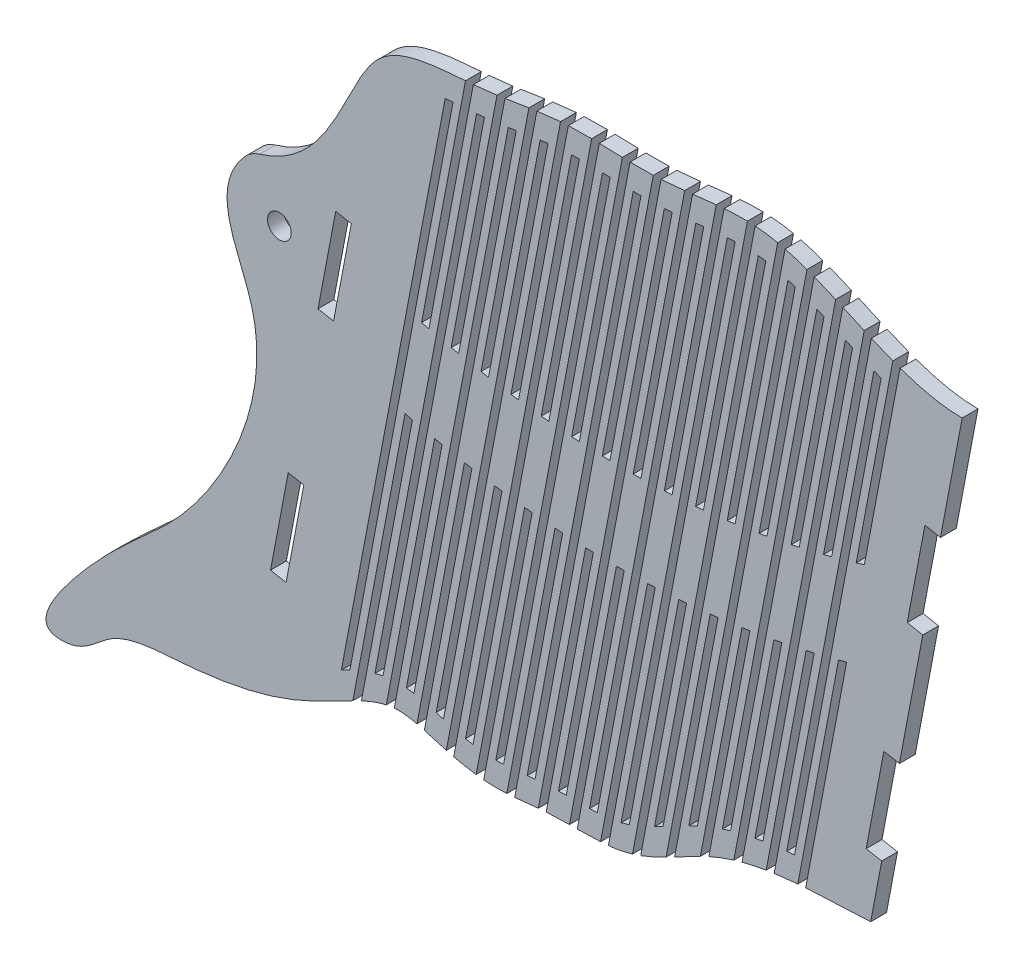
SolidWorks part; units mm, degrees
ref_plane "Front Plane" through (0, 0, 0) normal (0, 0, 1) x (1, 0, 0)
ref_plane "Top Plane" through (0, 0, 0) normal (0, 1, 0) x (1, 0, 0)
ref_plane "Right Plane" through (0, 0, 0) normal (1, 0, 0) x (0, 0, -1)
sketch "Sketch1" plane through (0, 0, 0) normal (0, 0, 1) x (1, 0, 0)
  line L0 (302.5, 350) -> (1512.5, 350) construction
  line L1 (262.9659, 222.1766) -> (281.3274, 318.909)
  line L2 (265.1799, 233.8401) -> (262.0606, 234.4322)
  line L3 (262.0606, 234.4322) -> (265.6131, 253.148)
  line L4 (265.6131, 253.148) -> (268.7324, 252.5559)
  line L5 (270.2997, 277.8379) -> (273.419, 277.2458)
  line L6 (270.2997, 277.8379) -> (273.8523, 296.5537)
  line L7 (273.8523, 296.5537) -> (276.9716, 295.9616)
  circle A0 centre (144.2993, 283.7368) radius 2.3813
  arc A1 (140.318, 294.2582) -> (137.3931, 292.395) centre (142.1375, 288.1744) ccw
  spline S0 degree 3 poles (140.318, 294.2582) (144.6102, 295.5419) (152.0973, 300.9004) (157.8753, 312.5659) (165.4859, 327.6166) (184.0324, 327.0096) (201.9177, 331.2233) (220.7397, 328.9762) (248.5279, 335.4047) (266.9458, 318.9101) (281.3274, 318.909) knots 0.008505 0.008505 0.008505 0.008505 0.084335 0.182889 0.2513 0.382138 0.48334 0.605315 0.73297 1 1 1 1
  spline S1 degree 3 poles (262.9659, 222.1766) (252.7762, 221.635) (234.6147, 222.0465) (215.7154, 207.8397) (199.7769, 209.3976) (187.3708, 207.1634) (177.2277, 209.3133) (167.4809, 212.7163) (157.835, 208.1386) (144.6841, 200.9083) (128.176, 197.8077) (111.1887, 197.5614) (105.0884, 189.8759) (93.8703, 189.645) (109.3047, 211.1797) (127.8117, 222.333) (145.742, 257.3878) (132.8133, 279.6418) (133.8098, 288.3669) (137.3931, 292.395) knots 0 0 0 0 0.108343 0.179805 0.231481 0.269558 0.310048 0.338876 0.372966 0.414981 0.496706 0.548446 0.578687 0.594262 0.641813 0.740934 0.901271 0.95171 0.994791 0.994791 0.994791 0.994791
  dimension "D1" = 6.35
  dimension "D10" = 4.7625
  dimension "D2" = 262.9659
  dimension "D3" = 281.3274
  dimension "D4" = 222.1766
  dimension "D5" = 318.909
  dimension "D6" = 3.175
  dimension "D7" = 3.175
  dimension "D8" = 19.05
  dimension "D9" = 19.05
extrude "Boss-Extrude1" add sketch "Sketch1" along normal blind 3.175 contours S1 L1 L2 L3 L4 L5 L6 L7 S0 A1 A0
sketch "Sketch2" plane through (0, 0, 3.175) normal (0, 0, 1) x (1, 0, 0)
  line L0 (255.132, 281.6956) -> (265.1753, 334.6059)
  line L1 (246.7613, 204.9081) -> (258.1468, 264.8897)
  line L2 (245.215, 204.934) -> (256.5109, 264.4431)
  line L3 (247.691, 226.15) -> (265.0641, 317.6756)
  line L4 (246.1113, 226) -> (263.6224, 318.2528)
  line L5 (240.5761, 205.0117) -> (251.6222, 263.205)
  line L6 (239.0298, 205.0376) -> (249.999, 262.8258)
  line L7 (241.3378, 225.3689) -> (259.32, 320.103)
  line L8 (239.7325, 225.0838) -> (257.89, 320.7417)
  line L9 (234.3909, 205.1154) -> (245.1483, 261.7877)
  line L10 (232.8446, 205.1413) -> (243.5376, 261.4744)
  line L11 (234.86, 223.9309) -> (253.5981, 322.6474)
  line L12 (233.213, 223.4259) -> (252.163, 323.2591)
  line L13 (228.2057, 205.219) -> (238.7239, 260.6311)
  line L14 (226.6595, 205.2449) -> (237.1254, 260.382)
  line L15 (228.1827, 221.4417) -> (247.8261, 324.9276)
  line L16 (226.4759, 220.6222) -> (246.3653, 325.4039)
  line L17 (222.0206, 205.3226) -> (232.3478, 259.7287)
  line L18 (220.4743, 205.3485) -> (230.7611, 259.542)
  line L19 (221.3104, 217.9258) -> (241.9148, 326.4739)
  line L20 (219.5905, 217.0368) -> (240.4024, 326.6783)
  line L21 (215.8354, 205.4262) -> (226.0187, 259.074)
  line L22 (214.2891, 205.4521) -> (224.4436, 258.9484)
  line L23 (214.5179, 214.8296) -> (235.7695, 326.7879)
  line L24 (212.8743, 214.3431) -> (234.2014, 326.6988)
  line L25 (209.6502, 205.5298) -> (219.7355, 258.6612)
  line L26 (208.1039, 205.5557) -> (218.1717, 258.5951)
  line L27 (208.0992, 213.7032) -> (229.4592, 326.2325)
  line L28 (206.5372, 213.6462) -> (227.8731, 326.0484)
  line L29 (203.465, 205.6334) -> (213.497, 258.4843)
  line L30 (201.9187, 205.6593) -> (211.9443, 258.4763)
  line L31 (201.8749, 213.6006) -> (223.1248, 325.55)
  line L32 (200.3182, 213.5718) -> (221.551, 325.4306)
  line L33 (197.2798, 205.737) -> (207.3024, 258.5379)
  line L34 (195.7335, 205.7629) -> (205.7604, 258.5866)
  line L35 (195.6074, 213.2705) -> (216.8695, 325.284)
  line L36 (194.0253, 213.1078) -> (215.32, 325.293)
  line L37 (191.0946, 205.8406) -> (201.1504, 258.8165)
  line L38 (189.5484, 205.8665) -> (199.619, 258.9207)
  line L39 (189.292, 212.688) -> (210.6879, 325.4063)
  line L40 (187.734, 212.6525) -> (209.1452, 325.4513)
  line L41 (184.9095, 205.9442) -> (195.0402, 259.315)
  line L42 (183.3632, 205.9701) -> (193.519, 259.4734)
  line L43 (183.1602, 213.0731) -> (204.5019, 325.5058)
  line L44 (181.663, 213.3573) -> (202.9437, 325.4688)
  line L45 (178.7243, 206.0478) -> (188.9708, 260.0285)
  line L46 (177.178, 206.0737) -> (187.4597, 260.2399)
  line L47 (177.2251, 214.4939) -> (198.2146, 325.0716)
  line L48 (175.7571, 214.9322) -> (196.6223, 324.8551)
  line L49 (172.5391, 206.1514) -> (182.9412, 260.9522)
  line L50 (170.9928, 206.1773) -> (181.44, 261.2154)
  line L51 (171.3115, 216.0286) -> (191.8264, 324.1054)
  line L52 (169.7979, 216.2265) -> (190.228, 323.8568)
  line L53 (166.3539, 206.255) -> (176.9507, 262.0815)
  line L54 (164.8076, 206.2809) -> (175.4591, 262.3954)
  line L55 (165.0985, 215.9856) -> (185.4558, 323.2324)
  line L56 (163.4741, 215.5998) -> (183.876, 323.0817)
  line L57 (160.1687, 206.3586) -> (170.9984, 263.412)
  line L58 (158.6224, 206.3845) -> (169.5162, 263.7755)
  line L59 (158.4486, 213.641) -> (179.1505, 322.7029)
  line L60 (156.7374, 212.798) -> (177.5717, 322.5575)
  line L61 (182.9611, 334.6059) -> (184.5123, 334.6059)
  line L62 (158.6224, 206.3845) -> (160.1687, 206.3586)
  line L63 (261.6993, 283.6048) -> (271.3802, 334.6059)
  line L64 (260.0521, 283.099) -> (269.829, 334.6059)
  line L65 (253.4991, 281.2652) -> (263.6241, 334.6059)
  line L66 (248.6213, 280.0842) -> (258.9705, 334.6059)
  line L67 (247.0023, 279.7267) -> (257.4193, 334.6059)
  line L68 (242.1653, 278.7609) -> (252.7656, 334.6059)
  line L69 (240.5596, 278.474) -> (251.2144, 334.6059)
  line L70 (235.7622, 277.7166) -> (246.5608, 334.6059)
  line L71 (234.1695, 277.498) -> (245.0096, 334.6059)
  line L72 (229.4104, 276.9424) -> (240.3559, 334.6059)
  line L73 (227.8303, 276.79) -> (238.8047, 334.6059)
  line L74 (223.1083, 276.43) -> (234.1511, 334.6059)
  line L75 (221.5404, 276.3419) -> (232.5999, 334.6059)
  line L76 (216.8544, 276.1716) -> (227.9462, 334.6059)
  line L77 (215.2983, 276.1458) -> (226.395, 334.6059)
  line L78 (210.6473, 276.1597) -> (221.7414, 334.6059)
  line L79 (209.1027, 276.1944) -> (220.1902, 334.6059)
  line L80 (204.4856, 276.3872) -> (215.5365, 334.6059)
  line L81 (202.9521, 276.4806) -> (213.9853, 334.6059)
  line L82 (198.3681, 276.8472) -> (209.3317, 334.6059)
  line L83 (196.8454, 276.9977) -> (207.7805, 334.6059)
  line L84 (192.2935, 277.5332) -> (203.1268, 334.6059)
  line L85 (190.7814, 277.7394) -> (201.5756, 334.6059)
  line L86 (186.2606, 278.4392) -> (196.922, 334.6059)
  line L87 (184.7587, 278.6994) -> (195.3708, 334.6059)
  line L88 (180.2683, 279.5591) -> (190.7171, 334.6059)
  line L89 (178.7765, 279.8719) -> (189.1659, 334.6059)
  line L90 (174.3156, 280.8874) -> (184.5123, 334.6059)
  line L91 (172.8335, 281.2514) -> (182.9611, 334.6059)
  line L92 (238.8047, 334.6059) -> (240.3559, 334.6059)
  line L93 (263.6241, 334.6059) -> (265.1753, 334.6059)
  line L94 (257.4193, 334.6059) -> (258.9705, 334.6059)
  line L95 (251.2144, 334.6059) -> (252.7656, 334.6059)
  line L96 (238.8047, 334.6059) -> (240.3559, 334.6059)
  line L97 (245.215, 204.934) -> (246.7613, 204.9081)
  line L98 (269.829, 334.6059) -> (271.3802, 334.6059)
  line L99 (189.1659, 334.6059) -> (190.7171, 334.6059)
  line L100 (195.3708, 334.6059) -> (196.922, 334.6059)
  line L101 (201.5756, 334.6059) -> (203.1268, 334.6059)
  line L102 (207.7805, 334.6059) -> (209.3317, 334.6059)
  line L103 (213.9853, 334.6059) -> (215.5365, 334.6059)
  line L104 (220.1902, 334.6059) -> (221.7414, 334.6059)
  line L105 (226.395, 334.6059) -> (227.9462, 334.6059)
  line L106 (232.5999, 334.6059) -> (234.1511, 334.6059)
  line L107 (245.0096, 334.6059) -> (246.5608, 334.6059)
  line L108 (239.0298, 205.0376) -> (240.5761, 205.0117)
  line L109 (232.8446, 205.1413) -> (234.3909, 205.1154)
  line L110 (226.6595, 205.2449) -> (228.2057, 205.219)
  line L111 (220.4743, 205.3485) -> (222.0206, 205.3226)
  line L112 (214.2891, 205.4521) -> (215.8354, 205.4262)
  line L113 (208.1039, 205.5557) -> (209.6502, 205.5298)
  line L114 (201.9187, 205.6593) -> (203.465, 205.6334)
  line L115 (195.7335, 205.7629) -> (197.2798, 205.737)
  line L116 (189.5484, 205.8665) -> (191.0946, 205.8406)
  line L117 (183.3632, 205.9701) -> (184.9095, 205.9442)
  line L118 (164.8076, 206.2809) -> (166.3539, 206.255)
  line L119 (170.9928, 206.1773) -> (172.5391, 206.1514)
  line L120 (177.178, 206.0737) -> (178.7243, 206.0478)
  spline S0 degree 3 poles (249.999, 262.8258) (250.5401, 262.9496) (251.0812, 263.076) (251.6222, 263.205) knots 0.751222 0.751222 0.751222 0.751222 0.764652 0.764652 0.764652 0.764652
  spline S1 degree 3 poles (253.4991, 281.2652) (254.0436, 281.4058) (254.5879, 281.5492) (255.132, 281.6956) knots 0.668788 0.668788 0.668788 0.668788 0.6809 0.6809 0.6809 0.6809
  spline S2 degree 3 poles (158.4486, 213.641) (157.8584, 213.36) (157.2888, 213.0764) (156.7374, 212.798) knots 0.659099 0.659099 0.659099 0.659099 0.669987 0.669987 0.669987 0.669987
  spline S3 degree 3 poles (171.3115, 216.0286) (170.8222, 216.1108) (170.3175, 216.1792) (169.7979, 216.2265) knots 0.593774 0.593774 0.593774 0.593774 0.601178 0.601178 0.601178 0.601178
  spline S5 degree 3 poles (165.0985, 215.9856) (164.9517, 215.9573) (164.8059, 215.9273) (164.2573, 215.808) (163.8617, 215.7086) (163.4741, 215.5998) knots 0.622873 0.622873 0.622873 0.622873 0.625 0.625 0.630938 0.630938 0.630938 0.630938
  spline S7 degree 3 poles (169.5162, 263.7755) (170.0104, 263.6522) (170.5044, 263.531) (170.9984, 263.412) knots 0.089065 0.089065 0.089065 0.089065 0.101194 0.101194 0.101194 0.101194
  spline S8 degree 3 poles (263.6224, 318.2528) (264.0996, 318.0573) (264.5801, 317.8646) (265.0641, 317.6756) knots 0.89658 0.89658 0.89658 0.89658 0.905747 0.905747 0.905747 0.905747
  spline S9 degree 3 poles (260.0521, 283.099) (260.6013, 283.2647) (261.1504, 283.4333) (261.6993, 283.6048) knots 0.717443 0.717443 0.717443 0.717443 0.729693 0.729693 0.729693 0.729693
  spline S10 degree 3 poles (256.5109, 264.4431) (257.0562, 264.5893) (257.6016, 264.7382) (258.1468, 264.8897) knots 0.80512 0.80512 0.80512 0.80512 0.818669 0.818669 0.818669 0.818669
  spline S11 degree 3 poles (247.0023, 279.7267) (247.5421, 279.8431) (248.0818, 279.9622) (248.6213, 280.0842) knots 0.620672 0.620672 0.620672 0.620672 0.632652 0.632652 0.632652 0.632652
  spline S12 degree 3 poles (243.5376, 261.4744) (244.0746, 261.5762) (244.6115, 261.6807) (245.1483, 261.7877) knots 0.697789 0.697789 0.697789 0.697789 0.711104 0.711104 0.711104 0.711104
  spline S13 degree 3 poles (237.1254, 260.382) (237.6583, 260.4625) (238.1912, 260.5455) (238.7239, 260.6311) knots 0.64481 0.64481 0.64481 0.64481 0.658013 0.658013 0.658013 0.658013
  spline S14 degree 3 poles (243.7743, 279.0652) (244.3119, 279.1697) (244.8493, 279.277) (245.3866, 279.3871) knots 0.596812 0.596812 0.596812 0.596812 0.608726 0.608726 0.608726 0.608726
  spline S15 degree 3 poles (240.5596, 278.474) (241.095, 278.5669) (241.6302, 278.6625) (242.1653, 278.7609) knots 0.573079 0.573079 0.573079 0.573079 0.584929 0.584929 0.584929 0.584929
  spline S16 degree 3 poles (224.4436, 258.9484) (224.9687, 258.9878) (225.4937, 259.0297) (226.0187, 259.074) knots 0.54017 0.54017 0.54017 0.54017 0.553157 0.553157 0.553157 0.553157
  spline S17 degree 3 poles (234.1695, 277.498) (234.7006, 277.5682) (235.2315, 277.641) (235.7622, 277.7166) knots 0.525991 0.525991 0.525991 0.525991 0.537716 0.537716 0.537716 0.537716
  spline S18 degree 3 poles (230.7611, 259.542) (231.2901, 259.6017) (231.819, 259.664) (232.3478, 259.7287) knots 0.592274 0.592274 0.592274 0.592274 0.605368 0.605368 0.605368 0.605368
  spline S19 degree 3 poles (227.8303, 276.79) (228.3571, 276.8382) (228.8838, 276.8889) (229.4104, 276.9424) knots 0.479392 0.479392 0.479392 0.479392 0.490997 0.490997 0.490997 0.490997
  spline S20 degree 3 poles (175.4591, 262.3954) (175.9564, 262.2886) (176.4536, 262.184) (176.9507, 262.0815) knots 0.137709 0.137709 0.137709 0.137709 0.149924 0.149924 0.149924 0.149924
  spline S21 degree 3 poles (221.5404, 276.3419) (222.0632, 276.3687) (222.5858, 276.398) (223.1083, 276.43) knots 0.433268 0.433268 0.433268 0.433268 0.444756 0.444756 0.444756 0.444756
  spline S22 degree 3 poles (218.1717, 258.5951) (218.693, 258.6147) (219.2143, 258.6367) (219.7355, 258.6612) knots 0.488488 0.488488 0.488488 0.488488 0.501369 0.501369 0.501369 0.501369
  spline S23 degree 3 poles (215.2983, 276.1458) (215.8171, 276.1519) (216.3358, 276.1605) (216.8544, 276.1716) knots 0.387605 0.387605 0.387605 0.387605 0.398978 0.398978 0.398978 0.398978
  spline S24 degree 3 poles (211.9443, 258.4763) (212.4619, 258.4766) (212.9795, 258.4792) (213.497, 258.4843) knots 0.437216 0.437216 0.437216 0.437216 0.449996 0.449996 0.449996 0.449996
  spline S25 degree 3 poles (209.1027, 276.1944) (209.6177, 276.1804) (210.1326, 276.1688) (210.6473, 276.1597) knots 0.342388 0.342388 0.342388 0.342388 0.353651 0.353651 0.353651 0.353651
  spline S26 degree 3 poles (190.7814, 277.7394) (191.2855, 277.6683) (191.7896, 277.5996) (192.2935, 277.5332) knots 0.209295 0.209295 0.209295 0.209295 0.220244 0.220244 0.220244 0.220244
  spline S27 degree 3 poles (202.9521, 276.4806) (203.4634, 276.447) (203.9746, 276.4159) (204.4856, 276.3872) knots 0.297606 0.297606 0.297606 0.297606 0.308762 0.308762 0.308762 0.308762
  spline S28 degree 3 poles (205.7604, 258.5866) (206.2744, 258.568) (206.7884, 258.5518) (207.3024, 258.5379) knots 0.386347 0.386347 0.386347 0.386347 0.399027 0.399027 0.399027 0.399027
  spline S29 degree 3 poles (196.8454, 276.9977) (197.3531, 276.9451) (197.8607, 276.895) (198.3681, 276.8472) knots 0.253245 0.253245 0.253245 0.253245 0.264297 0.264297 0.264297 0.264297
  spline S30 degree 3 poles (189.292, 212.688) (188.7678, 212.6629) (188.2578, 212.65) (187.7525, 212.6524) (187.7433, 212.6525) (187.734, 212.6525) knots 0.473119 0.473119 0.473119 0.473119 0.484375 0.484375 0.484584 0.484584 0.484584 0.484584
  spline S31 degree 3 poles (199.619, 258.9207) (200.1295, 258.8836) (200.64, 258.8489) (201.1504, 258.8165) knots 0.335869 0.335869 0.335869 0.335869 0.348452 0.348452 0.348452 0.348452
  spline S32 degree 3 poles (184.7587, 278.6994) (185.2595, 278.6103) (185.7601, 278.5236) (186.2606, 278.4392) knots 0.165743 0.165743 0.165743 0.165743 0.176594 0.176594 0.176594 0.176594
  spline S33 degree 3 poles (193.519, 259.4734) (194.0261, 259.4183) (194.5332, 259.3655) (195.0402, 259.315) knots 0.285775 0.285775 0.285775 0.285775 0.298263 0.298263 0.298263 0.298263
  spline S34 degree 3 poles (181.44, 261.2154) (181.9405, 261.1255) (182.4409, 261.0377) (182.9412, 260.9522) knots 0.186703 0.186703 0.186703 0.186703 0.199007 0.199007 0.199007 0.199007
  spline S35 degree 3 poles (178.7765, 279.8719) (179.2739, 279.7654) (179.7712, 279.6611) (180.2683, 279.5591) knots 0.122579 0.122579 0.122579 0.122579 0.133334 0.133334 0.133334 0.133334
  spline S36 degree 3 poles (177.2251, 214.4939) (177.0821, 214.5361) (176.9376, 214.579) (176.4556, 214.723) (176.111, 214.827) (175.7571, 214.9322) knots 0.55964 0.55964 0.55964 0.55964 0.5625 0.5625 0.569036 0.569036 0.569036 0.569036
  spline S37 degree 3 poles (172.8335, 281.2514) (173.3276, 281.1278) (173.8217, 281.0065) (174.3156, 280.8874) knots 0.079794 0.079794 0.079794 0.079794 0.090455 0.090455 0.090455 0.090455
  spline S38 degree 3 poles (187.4597, 260.2399) (187.9634, 260.1672) (188.4671, 260.0967) (188.9708, 260.0285) knots 0.236056 0.236056 0.236056 0.236056 0.248451 0.248451 0.248451 0.248451
  spline S39 degree 3 poles (201.8749, 213.6006) (201.3631, 213.5947) (200.844, 213.5858) (200.3182, 213.5718) knots 0.395679 0.395679 0.395679 0.395679 0.404839 0.404839 0.404839 0.404839
  spline S40 degree 3 poles (183.1602, 213.0731) (182.6655, 213.1568) (182.1664, 213.2518) (181.663, 213.3573) knots 0.518388 0.518388 0.518388 0.518388 0.529055 0.529055 0.529055 0.529055
  spline S41 degree 3 poles (195.6074, 213.2705) (195.2996, 213.2404) (194.9952, 213.2094) (194.4694, 213.1547) (194.2464, 213.1312) (194.0253, 213.1078) knots 0.43198 0.43198 0.43198 0.43198 0.4375 0.4375 0.441624 0.441624 0.441624 0.441624
  spline S42 degree 3 poles (221.3104, 217.9258) (220.7285, 217.6197) (220.1553, 217.3221) (219.5905, 217.0368) knots 0.254448 0.254448 0.254448 0.254448 0.266922 0.266922 0.266922 0.266922
  spline S43 degree 3 poles (208.0992, 213.7032) (207.5911, 213.6772) (207.0701, 213.659) (206.5372, 213.6462) knots 0.355873 0.355873 0.355873 0.355873 0.366464 0.366464 0.366464 0.366464
  spline S45 degree 3 poles (214.5179, 214.8296) (214.247, 214.7378) (213.9781, 214.6521) (213.4302, 214.4891) (213.1514, 214.4126) (212.8743, 214.3431) knots 0.305963 0.305963 0.305963 0.305963 0.3125 0.3125 0.319373 0.319373 0.319373 0.319373
  spline S46 degree 3 poles (228.1827, 221.4417) (227.6292, 221.1861) (227.0855, 220.9242) (226.5257, 220.6469) (226.5008, 220.6346) (226.4759, 220.6222) knots 0.208362 0.208362 0.208362 0.208362 0.21875 0.21875 0.219233 0.219233 0.219233 0.219233
  spline S48 degree 3 poles (234.86, 223.9309) (234.3101, 223.7729) (233.7609, 223.6049) (233.213, 223.4259) knots 0.16843 0.16843 0.16843 0.16843 0.178137 0.178137 0.178137 0.178137
  spline S50 degree 3 poles (241.3378, 225.3689) (240.8031, 225.2807) (240.2679, 225.1859) (239.7325, 225.0838) knots 0.130419 0.130419 0.130419 0.130419 0.139836 0.139836 0.139836 0.139836
  spline S51 degree 3 poles (257.89, 320.7417) (258.3638, 320.5294) (258.8404, 320.3162) (259.32, 320.103) knots 0.858868 0.858868 0.858868 0.858868 0.868458 0.868458 0.868458 0.868458
  spline S52 degree 3 poles (177.5717, 322.5575) (178.0879, 322.6096) (178.6149, 322.6575) (179.1505, 322.7029) knots 0.329494 0.329494 0.329494 0.329494 0.339364 0.339364 0.339364 0.339364
  spline S54 degree 3 poles (252.163, 323.2591) (252.6386, 323.0601) (253.1169, 322.8559) (253.5981, 322.6474) knots 0.819271 0.819271 0.819271 0.819271 0.829372 0.829372 0.829372 0.829372
  spline S55 degree 3 poles (247.691, 226.15) (247.1656, 226.1042) (246.639, 226.0544) (246.1113, 226) knots 0.092914 0.092914 0.092914 0.092914 0.102289 0.102289 0.102289 0.102289
  spline S56 degree 3 poles (246.3653, 325.4039) (246.546, 325.3483) (246.7272, 325.2913) (247.2134, 325.1349) (247.5191, 325.0331) (247.8261, 324.9276) knots 0.777218 0.777218 0.777218 0.777218 0.78125 0.78125 0.788011 0.788011 0.788011 0.788011
  spline S58 degree 3 poles (240.4024, 326.6783) (240.5155, 326.6665) (240.6287, 326.6539) (241.1313, 326.5942) (241.5222, 326.5386) (241.9148, 326.4739) knots 0.731725 0.731725 0.731725 0.731725 0.734375 0.734375 0.743474 0.743474 0.743474 0.743474
  spline S60 degree 3 poles (234.2014, 326.6988) (234.2553, 326.7026) (234.3092, 326.7064) (234.838, 326.7426) (235.3069, 326.7689) (235.7695, 326.7879) knots 0.68639 0.68639 0.68639 0.68639 0.6875 0.6875 0.697305 0.697305 0.697305 0.697305
  spline S62 degree 3 poles (227.8731, 326.0484) (228.4072, 326.1104) (228.9359, 326.1723) (229.4592, 326.2325) knots 0.645047 0.645047 0.645047 0.645047 0.655063 0.655063 0.655063 0.655063
  spline S64 degree 3 poles (221.551, 325.4306) (221.6914, 325.4397) (221.8315, 325.4492) (222.358, 325.4868) (222.7426, 325.5172) (223.1248, 325.55) knots 0.606921 0.606921 0.606921 0.606921 0.609375 0.609375 0.616169 0.616169 0.616169 0.616169
  spline S66 degree 3 poles (215.32, 325.293) (215.833, 325.2866) (216.3495, 325.2832) (216.8695, 325.284) knots 0.570205 0.570205 0.570205 0.570205 0.579504 0.579504 0.579504 0.579504
  spline S68 degree 3 poles (209.1452, 325.4513) (209.655, 325.4374) (210.1693, 325.422) (210.6879, 325.4063) knots 0.53175 0.53175 0.53175 0.53175 0.541589 0.541589 0.541589 0.541589
  spline S70 degree 3 poles (202.9437, 325.4688) (203.4089, 325.4859) (203.8792, 325.4973) (204.4035, 325.5046) (204.4527, 325.5053) (204.5019, 325.5058) knots 0.490247 0.490247 0.490247 0.490247 0.5 0.5 0.501008 0.501008 0.501008 0.501008
  spline S72 degree 3 poles (196.6223, 324.8551) (197.1589, 324.9326) (197.6894, 325.0052) (198.2146, 325.0716) knots 0.445939 0.445939 0.445939 0.445939 0.456854 0.456854 0.456854 0.456854
  spline S74 degree 3 poles (190.228, 323.8568) (190.3174, 323.8704) (190.4066, 323.884) (190.9441, 323.9663) (191.3875, 324.0358) (191.8264, 324.1054) knots 0.404602 0.404602 0.404602 0.404602 0.40625 0.40625 0.41455 0.41455 0.41455 0.41455
  spline S76 degree 3 poles (183.876, 323.0817) (184.3186, 323.1206) (184.7637, 323.162) (185.2924, 323.2155) (185.3741, 323.2239) (185.4558, 323.2324) knots 0.367354 0.367354 0.367354 0.367354 0.375 0.375 0.376398 0.376398 0.376398 0.376398
  dimension "D2" = 60
extrude "Cut-Extrude1" cut sketch "Sketch2" against normal blind 3.175 contours L73 S19 L72 L6 | L92 L73 L6 L72 | L75 S21 L74 L6 | L106 L75 L6 L74 | L77 S23 L76 L6 | L105 L77 L6 L76 | L79 S25 L78 L6 | L104 L79 L6 L78 | L81 S27 L80 L6 | L103 L81 L6 L80 | L83 S29 L82 L6 | L102 L83 L6 L82 | L85 S26 L84 L6 | L101 L85 L6 L84 | S10 L2 S52 L1 | L2 L97 L1 S52 | L18 L111 L17 S52 | S18 L18 S52 L17 | S31 L38 S52 L37 | L38 L116 L37 S52 | S52 L60 S2 L59 | S76 L56 S5 L55 | S74 L52 S3 L51 | S72 L48 S36 L47 | S70 L44 S40 L43 | S68 L40 S30 L39 | S66 L36 S41 L35 | S64 L32 S39 L31 | S62 L28 S43 L27 | S60 L24 S45 L23 | S58 L20 S42 L19 | S56 L16 S46 L15 | S48 L11 S14 L12 | S51 L8 S50 L7 | S55 L3 S8 L4 | L63 L98 L64 S9 | L0 L93 L65 S1 | L67 L94 L66 S11 | L68 L95 L69 S15 | L71 L107 L70 S17 | L87 L100 L86 S32 | L89 L99 L88 S35 | L91 L61 L90 S37 | L9 S12 L10 L109 | L13 S13 L14 L110 | L21 S16 L22 L112 | L26 S22 L25 L113 | L29 S24 L30 L114 | L33 S28 L34 L115 | L41 S33 L42 L117 | L45 S38 L46 L120 | L49 S34 L50 L119 | L53 S20 L54 L118 | L57 S7 L58 L62
sketch "Sketch3" plane through (0, 0, 3.175) normal (0, 0, 1) x (1, 0, 0)
  line L0 (142.5285, 223.0685) -> (145.6478, 222.4764)
  line L1 (145.6478, 222.4764) -> (149.2003, 241.1922)
  line L2 (149.2003, 241.1922) -> (146.081, 241.7843)
  line L3 (146.081, 241.7843) -> (142.5285, 223.0685)
  line L4 (142.5285, 223.0685) -> (143.6889, 228.6284)
  line L5 (152.0563, 273.2632) -> (155.1756, 272.6711)
  line L6 (155.1756, 272.6711) -> (158.7282, 291.3869)
  line L7 (158.7282, 291.3869) -> (155.6089, 291.979)
  line L8 (155.6089, 291.979) -> (152.0563, 273.2632)
  line L9 (152.0563, 273.2632) -> (152.9488, 278.2735)
  line L10 (156.7374, 212.798) -> (177.5717, 322.5575) construction
  dimension "D1" = 3.175
  dimension "D2" = 3.175
  dimension "D3" = 19.05
  dimension "D4" = 19.05
  dimension "D5" = 12.7
  dimension "D6" = 12.7
extrude "Cut-Extrude2" cut sketch "Sketch3" against normal blind 5.08
